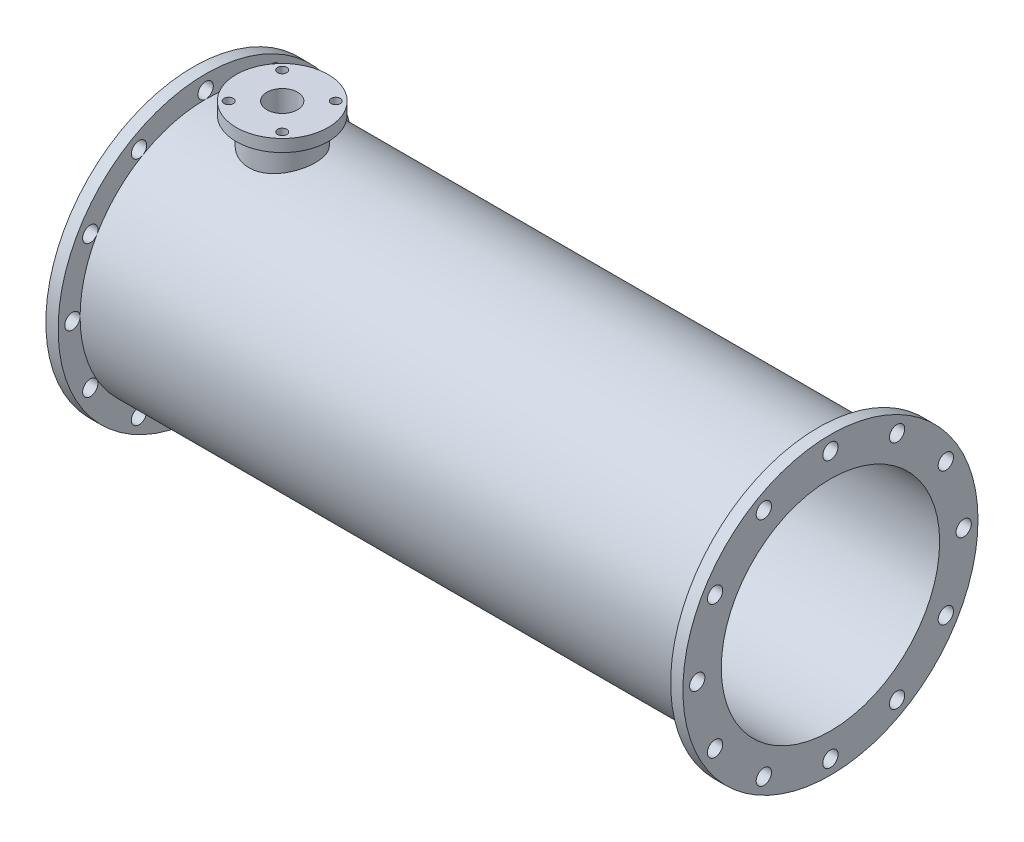
SolidWorks part; units mm, degrees
ref_plane "Front Plane" through (0, 0, 0) normal (0, 0, 1) x (1, 0, 0)
ref_plane "Top Plane" through (0, 0, 0) normal (0, 1, 0) x (1, 0, 0)
ref_plane "Right Plane" through (0, 0, 0) normal (1, 0, 0) x (0, 0, -1)
sketch "Sketch1" plane through (0, 0, 0) normal (1, 0, 0) x (0, 0, -1)
  circle A0 centre (0, 0) radius 2408.8383
  circle A1 centre (0, 0) radius 1782.5403
  circle A2 centre (0, 0) radius 2175 construction
  circle A3 centre (0, 2175) radius 125
  circle A4 centre (1087.5, 1883.6053) radius 125
  circle A5 centre (1883.6053, 1087.5) radius 125
  circle A6 centre (2175, 0) radius 125
  circle A7 centre (1883.6053, -1087.5) radius 125
  circle A8 centre (1087.5, -1883.6053) radius 125
  circle A9 centre (0, -2175) radius 125
  circle A10 centre (-1087.5, -1883.6053) radius 125
  circle A11 centre (-1883.6053, -1087.5) radius 125
  circle A12 centre (-2175, 0) radius 125
  circle A13 centre (-1883.6053, 1087.5) radius 125
  circle A14 centre (-1087.5, 1883.6053) radius 125
  point P31 (0, 0)
  dimension "D1" = 4350
  dimension "D2" = 12
extrude "Boss-Extrude1" add sketch "Sketch1" along normal blind 200
sketch "Sketch2" plane through (200, 0, 0) normal (1, 0, 0) x (0, 0, -1)
  circle A0 centre (0, 0) radius 1782.5403
  circle A1 centre (0, 0) radius 2050
extrude "Boss-Extrude3" add sketch "Sketch2" along normal blind 2500
ref_plane "Plane2" through (1450, 0, 0) normal (1, 0, 0) x (0, 0, -1)
ref_plane "Plane3" through (0, 2650, 0) normal (0, 1, 0) x (1, 0, 0)
sketch "Sketch4" plane through (0, 2650, 0) normal (0, 1, 0) x (1, 0, 0)
  line L0 (1450, -2649.7221) -> (1450, 2649.7221) construction
  line L1 (1450, 0) -> (3344.1167, 0) construction
  line L2 (1450, 0) -> (3390.7436, 1940.7436) construction
  circle A0 centre (1450, 0) radius 750
  circle A1 centre (1450, 0) radius 625 construction
  circle A4 centre (1887.093, 437.093) radius 75
  circle A5 centre (1887.093, -437.093) radius 75
  circle A6 centre (1012.907, -437.093) radius 75
  circle A7 centre (1012.907, 437.093) radius 75
  point P21 (1450, 0)
  dimension "D1" = 1500
  dimension "D2" = 1250
  dimension "D4" = 4
  dimension "D3" = 45
extrude "Boss-Extrude15" add sketch "Sketch4" against normal blind 200 separate body contours A6 | A0 | A5 | A4 | A7
sketch "Sketch11" plane through (0, 2650, 0) normal (0, 1, 0) x (1, 0, 0)
  circle A0 centre (1450, 0) radius 543.1428
  circle A1 centre (1450, 0) radius 250
  dimension "D1" = 500
extrude "Boss-Extrude17" add sketch "Sketch11" against normal up to surface contours A1 | A0
sketch "Sketch12" plane through (0, 2650, 0) normal (0, 1, 0) x (1, 0, 0)
  line L0 (1450, -2649.7221) -> (1450, 2649.7221) construction
  circle A0 centre (1450, 0) radius 250
  dimension "D1" = 500
extrude "Cut-Extrude4" cut sketch "Sketch12" against normal blind 1310
sketch "Sketch13" plane through (0, 2650, 0) normal (0, 1, 0) x (1, 0, 0)
  circle A0 centre (1450, 0) radius 250
  point P3 (0, 0)
sketch "Sketch14" plane through (2700, 0, 0) normal (1, 0, 0) x (0, 0, -1)
  circle A0 centre (0, 0) radius 2050
  circle A1 centre (0, 0) radius 1782.5403
extrude "Boss-Extrude18" add sketch "Sketch14" along normal blind 7500
ref_plane "Plane4" through (5200, 0, 0) normal (1, 0, 0) x (0, 0, -1)
mirror "Mirror5" about plane through (5200, 0, 0) normal (1, 0, 0) of "Boss-Extrude1"
ref_plane "Plane5" through (0, -3350, 0) normal (0, 1, 0) x (1, 0, 0)
sketch "Sketch21" plane through (0, 0, 0) normal (0, 0, 1) x (1, 0, 0)
  line L0 (10400, 2408.8383) -> (0, -2408.8383)
ref_plane "Plane8" through (918.7184, -1983.2529, 0.0066) normal (0.4203, -0.9074, 0) x (-0.9074, -0.4203, 0)
